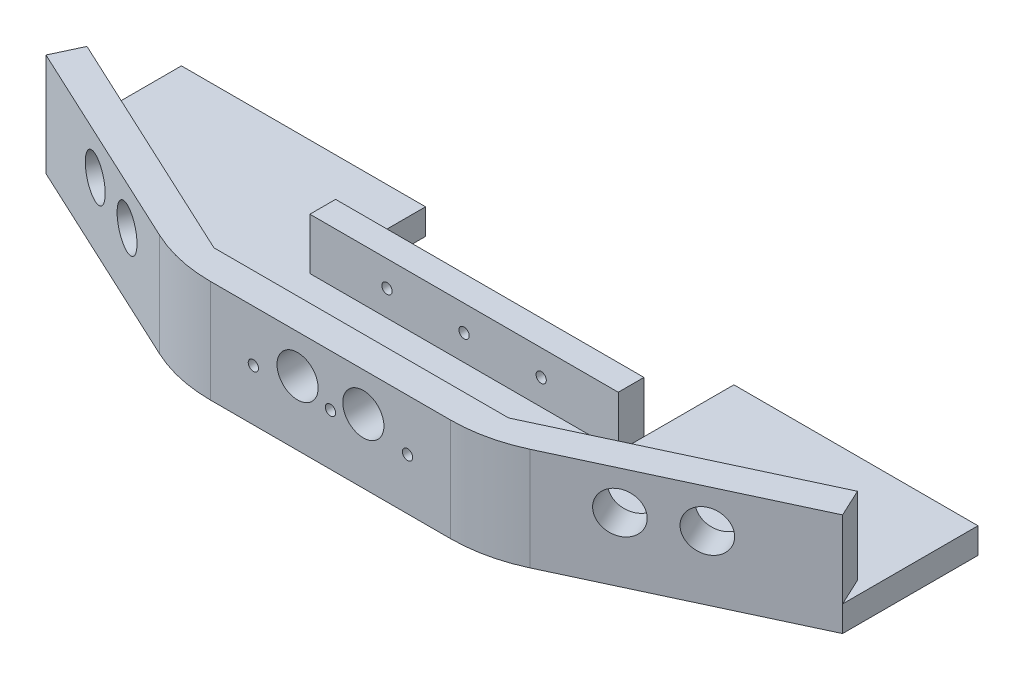
SolidWorks part; units mm, degrees
ref_plane "前视基准面" through (0, 0, 0) normal (0, 0, 1) x (1, 0, 0)
ref_plane "上视基准面" through (0, 0, 0) normal (0, 1, 0) x (1, 0, 0)
ref_plane "右视基准面" through (0, 0, 0) normal (1, 0, 0) x (0, 0, -1)
sketch "Sketch1" plane through (0, 0, 0) normal (0, 1, 0) x (1, 0, 0)
  line L0 (-60, 0) -> (60, 0)
  line L1 (60, 0) -> (155, 44.2992)
  line L2 (0, 0) -> (0, 297.9747) construction
  line L3 (-60, 0) -> (-155, 44.2992)
  point P4 (0, 0)
  dimension "D1" = 120
  dimension "D2" = 155
  dimension "D3" = 95
extrude "Extrude-Thin1" add sketch "Sketch1" along normal blind 30 thin thin type one direction wall 12
sketch "Sketch2" plane through (10.7164, 0, 22.9813) normal (0.4226, 0, 0.9063) x (0.9063, 0, -0.4226)
  line L0 (106.7889, 30) -> (106.7889, 0) construction
  line L1 (159.1994, 30) -> (54.3785, 30) construction
  line L2 (159.1994, 0) -> (54.3785, 0) construction
  line L3 (93.9889, 15) -> (119.5889, 15) construction
  circle A0 centre (93.9889, 15) radius 8
  circle A1 centre (119.5889, 15) radius 8
  point P9 (106.7889, 15)
  dimension "D2" = 16
  dimension "D3" = 16
  dimension "D1" = 25.6
extrude "Cut-Extrude1" cut sketch "Sketch2" against normal through all
mirror "Mirror1" about plane through (0, 0, 0) normal (1, 0, 0) of "Cut-Extrude1"
sketch "Sketch3" plane through (0, 0, 0) normal (0, 0, 1) x (1, 0, 0)
  line L0 (0, 0) -> (0, 30) construction
  line L1 (60, 30) -> (-60, 30) construction
  line L2 (-12.8, 15) -> (12.8, 15) construction
  circle A0 centre (12.8, 15) radius 8
  circle A1 centre (-12.8, 15) radius 8
  point P8 (0, 15)
  dimension "D2" = 16
  dimension "D1" = 25.6
extrude "Cut-Extrude2" cut sketch "Sketch3" against normal through all
sketch "Sketch4" plane through (0, 30, 0) normal (0, 1, 0) x (1, 0, 0)
  line L0 (0, 0) -> (0, -1000) construction
  line L1 (0, 0) -> (-267.9492, -1000) construction
  line L2 (0, 0) -> (267.9492, -1000) construction
  line L3 (60.3367, -1000) -> (-60.3367, -1000)
  line L4 (-60, 0) -> (-60, -1000) construction
  line L5 (60, 0) -> (60, -1000) construction
  line L6 (107.5, 22.1496) -> (530.1183, -884.1582) construction
  line L7 (155, 44.2992) -> (60, 0) construction
  line L8 (287.2731, -997.3987) -> (772.9634, -770.9176)
  point P8 (0, -1000)
  point P22 (530.1183, -884.1582)
  dimension "D1" = 15
  dimension "D2" = 15
  dimension "D3" = 1000
  dimension "D4" = 535.9
  dimension "D5" = 1000
sketch "Sketch5" plane through (0, 0, 0) normal (0, -1, 0) x (1, 0, 0)
  line L0 (0, 0) -> (0, -53.5875) construction
  line L1 (0, 0) -> (0, 1000) construction
  line L2 (149.9286, -55.1749) -> (-149.9286, -55.1749)
  line L3 (-60, -52) -> (60, -52)
  line L4 (-60, -52) -> (-60, -55.1749)
  line L5 (-60, -55.1749) -> (60, -55.1749)
  line L6 (60, -52) -> (60, -55.1749)
  line L7 (-60, -52) -> (60, -55.1749) construction
  line L8 (-60, -55.1749) -> (60, -52) construction
  line L9 (60, -52) -> (66.8086, -55.1749)
  line L10 (149.9286, -55.1749) -> (57.3397, -12) construction
  line L11 (57.3397, -12) -> (-57.3397, -12) construction
  line L12 (-60, -52) -> (-66.8086, -55.1749)
  line M8 (-149.9286, -55.1749) -> (-57.3397, -12)
  line M9 (-57.3397, -12) -> (57.3397, -12)
  line M10 (57.3397, -12) -> (149.9286, -55.1749)
  line M11 (149.9286, -55.1749) -> (155, -44.2992)
  line M12 (155, -44.2992) -> (60, 0)
  line M13 (60, 0) -> (-60, 0)
  line M14 (-60, 0) -> (-155, -44.2992)
  line M15 (-155, -44.2992) -> (-149.9286, -55.1749)
  dimension "D1" = 120
  dimension "D2" = 40
extrude "Boss-Extrude1" add sketch "Sketch5" along normal blind 10 contours L12 L3 L9 L2 M10 M9 M8 | M15 M8 M9 M10 M11 M12 M13 M14
sketch "Sketch7" plane through (0, 0, -52) normal (0, 0, -1) x (-1, 0, 0)
  line L0 (60, -10) -> (60, 0) construction
  line L1 (-60, -10) -> (60, -10)
  line L2 (-60, -10) -> (-60, 20)
  line L3 (-60, 20) -> (60, 20)
  line L4 (60, -10) -> (60, 20)
  line L5 (-57.3397, 0) -> (57.3397, 0) construction
  dimension "D1" = 20
extrude "Boss-Extrude2" add sketch "Sketch7" along normal blind 10
sketch "Sketch8" plane through (0, 0, -62) normal (0, 0, -1) x (-1, 0, 0)
  line L0 (-60, 10) -> (60, 10) construction
  line L1 (-60, 20) -> (-60, -10) construction
  line L2 (60, -10) -> (60, 20) construction
  line L3 (60, 20) -> (-60, 20) construction
  line L4 (0, 10) -> (0, 0) construction
  circle A0 centre (0, 10) radius 2
  circle A1 centre (-30, 10) radius 2
  circle A2 centre (30, 10) radius 2
  dimension "D2" = 4
  dimension "D3" = 4
  dimension "D4" = 30
  dimension "D1" = 10
extrude "Cut-Extrude3" cut sketch "Sketch8" against normal through all
sketch "Sketch9" plane through (0, 0, 0) normal (0, 1, 0) x (1, 0, 0)
  line L0 (-60, 62) -> (-60, 97) construction
  line L1 (60, 62) -> (60, 97) construction
  line L2 (60, 97) -> (-60, 97) construction
  line L3 (0, 0) -> (0, 97) construction
  line L4 (60, 97) -> (155, 97)
  line L5 (60, 97) -> (60, 44.2992)
  line L6 (60, 44.2992) -> (155, 44.2992)
  line L7 (155, 97) -> (155, 44.2992)
  dimension "D1" = 35
fillet "Fillet1" radius 60 2 edges at (-60, 10, 0) (60, 10, 0)
extrude "Boss-Extrude3" add sketch "Sketch9" against normal blind 10
mirror "Mirror2" about plane through (0, 0, 0) normal (1, 0, 0) of "Boss-Extrude3"
sketch "Sketch10" plane through (5.645, 0, 12.1056) normal (-0.4226, 0, -0.9063) x (-0.9063, 0, 0.4226)
  line L0 (-106.7889, 30) -> (-106.7889, 0) construction
  line L1 (161.1611, 30) -> (-374.7389, 30) construction
  line L2 (-95.3724, 0) -> (-181.4717, 0) construction
  line L3 (-159.1994, 0) -> (-57.0388, 0) construction
  line L4 (-112.2889, 21.3) -> (-101.2889, 21.3)
  line L5 (-112.2889, 21.3) -> (-112.2889, 25.3)
  line L6 (-112.2889, 25.3) -> (-101.2889, 25.3)
  line L7 (-101.2889, 21.3) -> (-101.2889, 25.3)
  line L8 (-112.2889, 21.3) -> (-101.2889, 25.3) construction
  line L9 (-112.2889, 25.3) -> (-101.2889, 21.3) construction
  line L10 (-112.2889, 4.7) -> (-101.2889, 4.7)
  line L11 (-112.2889, 4.7) -> (-112.2889, 9.7)
  line L12 (-112.2889, 9.7) -> (-101.2889, 9.7)
  line L13 (-101.2889, 4.7) -> (-101.2889, 9.7)
  line L14 (-112.2889, 4.7) -> (-101.2889, 9.7) construction
  line L15 (-112.2889, 9.7) -> (-101.2889, 4.7) construction
  point P6 (-106.7889, 23.3)
  point P11 (-106.7889, 7.2)
  dimension "D1" = 11
  dimension "D2" = 4
  dimension "D3" = 4.7
  dimension "D4" = 5
  dimension "D5" = 11
  dimension "D6" = 4.7
extrude "Cut-Extrude4" cut sketch "Sketch10" against normal blind 4.5
mirror "Mirror3" about plane through (0, 0, 0) normal (1, 0, 0) of "Cut-Extrude4"
sketch "Sketch13" plane through (0, 0, -12) normal (0, 0, -1) x (-1, 0, 0)
  line L0 (0, 0) -> (0, 30) construction
  line L1 (-60.3367, 30) -> (60.3367, 30) construction
  line L3 (-5.5, 4.7) -> (5.5, 4.7)
  line L4 (-5.5, 4.7) -> (-5.5, 9.7)
  line L5 (-5.5, 9.7) -> (5.5, 9.7)
  line L6 (5.5, 4.7) -> (5.5, 9.7)
  line L7 (-5.5, 4.7) -> (5.5, 9.7) construction
  line L8 (-5.5, 9.7) -> (5.5, 4.7) construction
  line L9 (-5.5, 25.3) -> (5.5, 25.3)
  line L10 (-5.5, 25.3) -> (-5.5, 21.3)
  line L11 (-5.5, 21.3) -> (5.5, 21.3)
  line L12 (5.5, 25.3) -> (5.5, 21.3)
  line L13 (-5.5, 25.3) -> (5.5, 21.3) construction
  line L14 (-5.5, 21.3) -> (5.5, 25.3) construction
  line L15 (-149.9286, 0) -> (-57.3397, 0) construction
  point P5 (0, 7.2)
  point P10 (0, 23.3)
  dimension "D1" = 4.7
  dimension "D2" = 4.7
  dimension "D3" = 5
  dimension "D4" = 11
  dimension "D5" = 11
  dimension "D6" = 4
extrude "Cut-Extrude5" cut sketch "Sketch13" against normal blind 4
